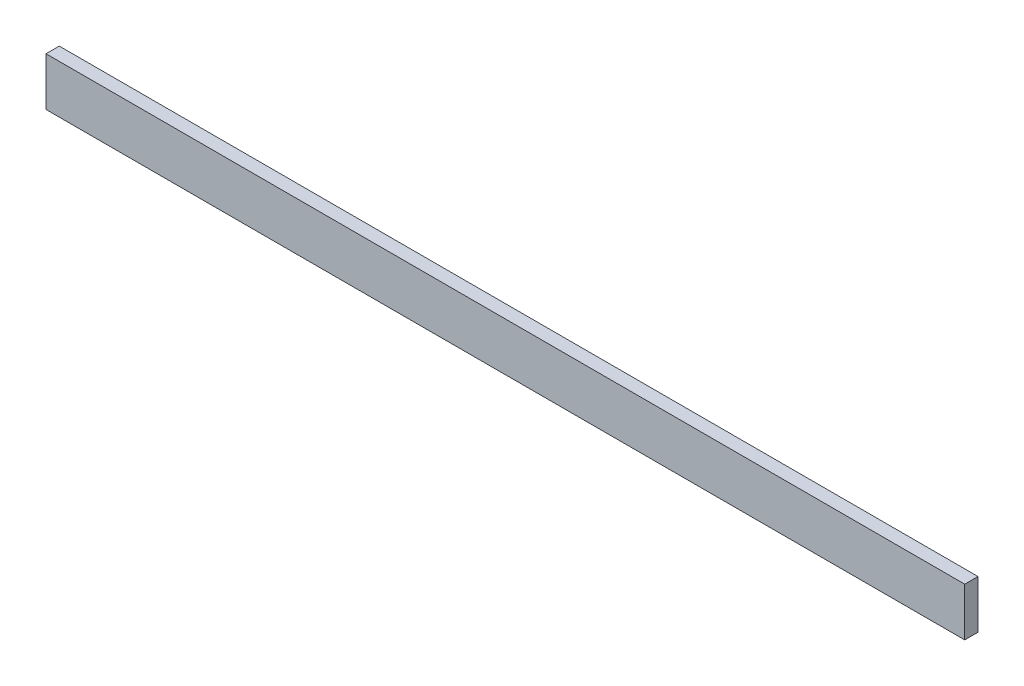
SolidWorks part; units mm, degrees
ref_plane "Plan de face" through (0, 0, 0) normal (0, 0, 1) x (1, 0, 0)
ref_plane "Plan de dessus" through (0, 0, 0) normal (0, 1, 0) x (1, 0, 0)
ref_plane "Plan de droite" through (0, 0, 0) normal (1, 0, 0) x (0, 0, -1)
sketch "Esquisse1" plane through (0, 0, 0) normal (0, 0, 1) x (1, 0, 0)
  line L1 (0, 0) -> (1522, 0)
  line L2 (0, 0) -> (0, 80)
  line L3 (0, 80) -> (1522, 80)
  line L4 (1522, 0) -> (1522, 80)
  dimension "D1" = 1522
  dimension "D2" = 80
extrude "Extrusion1" add sketch "Esquisse1" along normal blind 22
